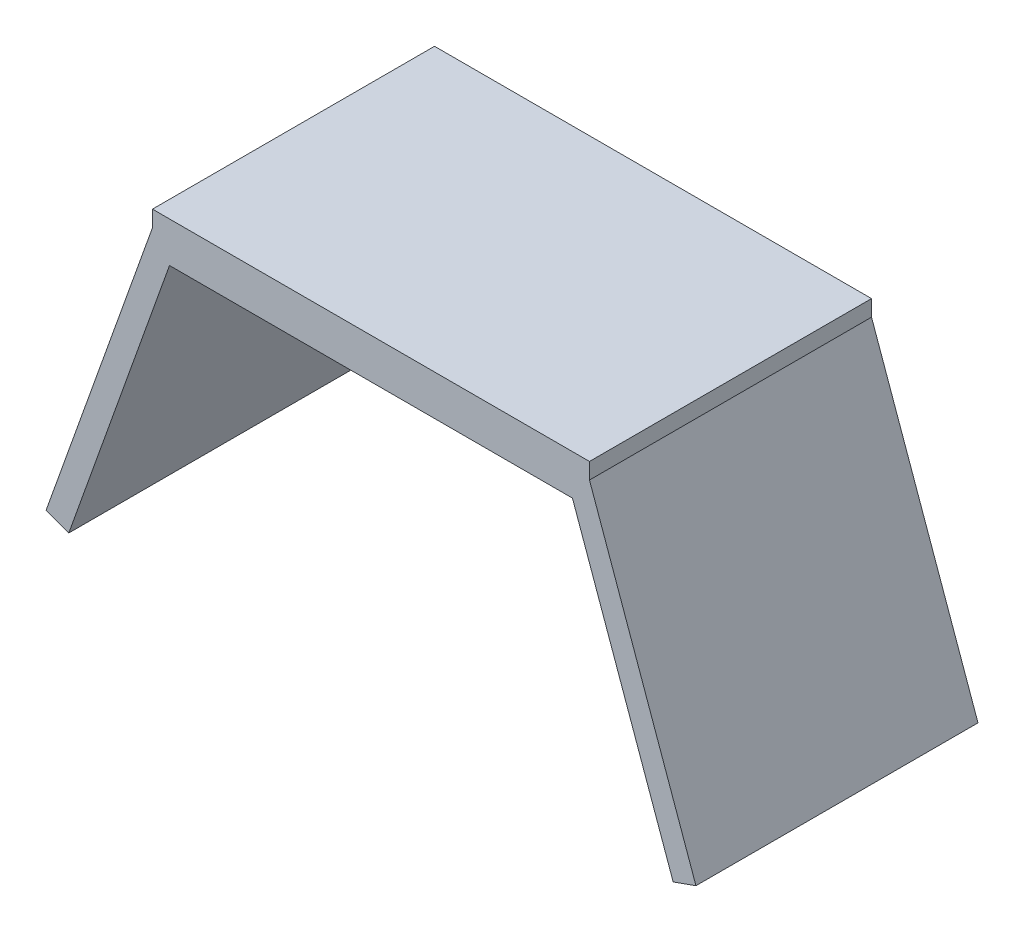
SolidWorks part; units mm, degrees
ref_plane "Front Plane" through (0, 0, 0) normal (0, 0, 1) x (1, 0, 0)
ref_plane "Top Plane" through (0, 0, 0) normal (0, 1, 0) x (1, 0, 0)
ref_plane "Right Plane" through (0, 0, 0) normal (1, 0, 0) x (0, 0, -1)
sketch "Sketch2" plane through (0, 0, 0) normal (0, 0, 1) x (1, 0, 0)
  line L0 (0, 15.5556) -> (0, -18.5149) construction
  line L1 (-25, 0) -> (25, 0)
  line L4 (25, 0) -> (37.5, -35)
  line L5 (-25, 0) -> (-37.5, -35)
  line L6 (27.1142, 3) -> (40.3252, -33.991)
  line L8 (-27.1142, 3) -> (-40.3252, -33.991)
  line L9 (37.5, -35) -> (40.3252, -33.991)
  line L10 (-37.5, -35) -> (-40.3252, -33.991)
  line L11 (-27.1142, 3) -> (-27.1142, 5)
  line L12 (-27.1142, 5) -> (27.1142, 5)
  line L14 (27.1142, 3) -> (27.1142, 5)
  line L15 (-27.1142, 3) -> (27.1142, 3) construction
  line L16 (0, -18.5149) -> (0, -62.5451) construction
  dimension "D1" = 25
  dimension "D2" = 50
  dimension "D3" = 3
  dimension "D4" = 35
  dimension "D5" = 37.5
  dimension "D6" = 5
  dimension "D8" = 37.5
  dimension "D9" = 109.654
extrude "Boss-Extrude2" add sketch "Sketch2" along normal blind 35
